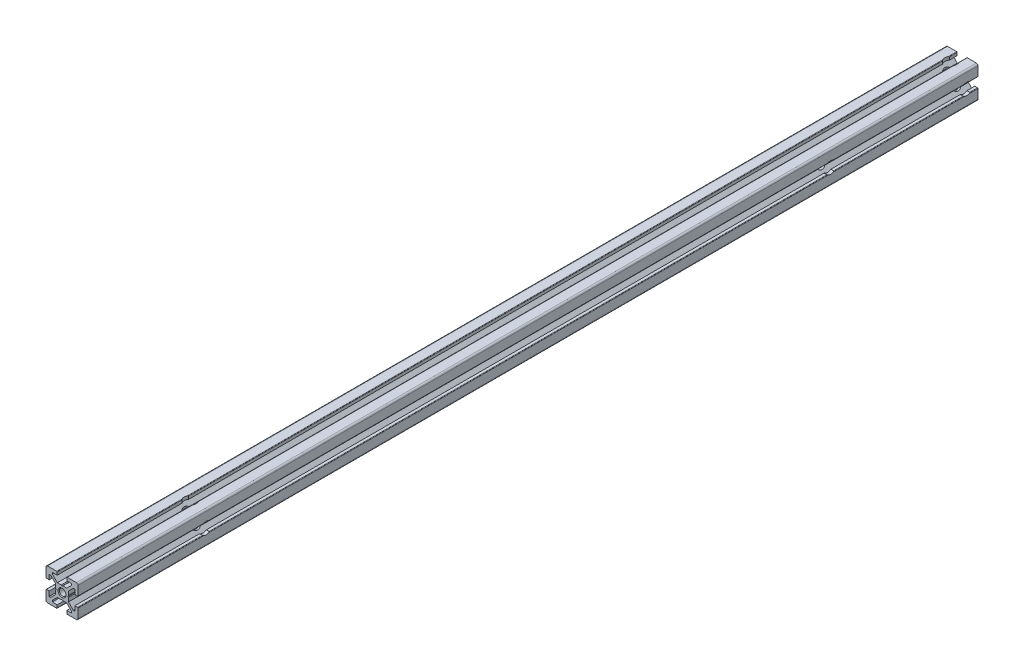
SolidWorks part; units mm, degrees
material "6063-T5"
ref_plane "Front Plane" through (0, 0, 0) normal (0, 0, 1) x (1, 0, 0)
ref_plane "Top Plane" through (0, 0, 0) normal (0, 1, 0) x (1, 0, 0)
ref_plane "Right Plane" through (0, 0, 0) normal (1, 0, 0) x (0, 0, -1)
ref_plane "Plane1" through (0, 0, 0) normal (0, 0, 1) x (1, 0, 0)
sketch "Sketch1" plane through (0, 0, 0) normal (0, 0, 1) x (1, 0, 0)
  line L0 (-10, 9) -> (-10, 3.3)
  line L1 (-9.7, 3) -> (-8, 3)
  line L2 (-8, 3) -> (-8, 6)
  line L3 (-8, 6) -> (-7.0607, 6)
  line L4 (-7.0607, 6) -> (-4, 2.9393)
  line L5 (-4, 2.9393) -> (-4, 0.5196)
  line L6 (-4, 0.5196) -> (-3.7, 0)
  line L7 (-3.7, 0) -> (-4, -0.5196)
  line L8 (-4, -0.5196) -> (-4, -2.9393)
  line L9 (-4, -2.9393) -> (-7.0607, -6)
  line L10 (-7.0607, -6) -> (-8, -6)
  line L11 (-8, -6) -> (-8, -3)
  line L12 (-8, -3) -> (-9.7, -3)
  line L13 (-10, -3.3) -> (-10, -9)
  line L14 (-9, -10) -> (-3.3, -10)
  line L15 (-3, -9.7) -> (-3, -8)
  line L16 (-3, -8) -> (-6, -8)
  line L17 (-6, -8) -> (-6, -7.0607)
  line L18 (-6, -7.0607) -> (-2.9393, -4)
  line L19 (-2.9393, -4) -> (-0.5196, -4)
  line L20 (-0.5196, -4) -> (0, -3.7)
  line L21 (0, -3.7) -> (0.5196, -4)
  line L22 (0.5196, -4) -> (2.9393, -4)
  line L23 (2.9393, -4) -> (6, -7.0607)
  line L24 (6, -7.0607) -> (6, -8)
  line L25 (6, -8) -> (3, -8)
  line L26 (3, -8) -> (3, -9.7)
  line L27 (3.3, -10) -> (9, -10)
  line L28 (10, -9) -> (10, -3.3)
  line L29 (9.7, -3) -> (8, -3)
  line L30 (8, -3) -> (8, -6)
  line L31 (8, -6) -> (7.0606, -6)
  line L32 (7.0606, -6) -> (4, -2.9393)
  line L33 (4, -2.9393) -> (4, -0.5196)
  line L34 (4, -0.5196) -> (3.7, 0)
  line L35 (3.7, 0) -> (4, 0.5196)
  line L36 (4, 0.5196) -> (4, 2.9393)
  line L37 (4, 2.9393) -> (7.0607, 6)
  line L38 (7.0607, 6) -> (8, 6)
  line L39 (8, 6) -> (8, 3)
  line L40 (8, 3) -> (9.7, 3)
  line L41 (10, 3.3) -> (10, 9)
  line L42 (9, 10) -> (3.3, 10)
  line L43 (3, 9.7) -> (3, 8)
  line L44 (3, 8) -> (6, 8)
  line L45 (6, 8) -> (6, 7.0607)
  line L46 (6, 7.0607) -> (2.9393, 4)
  line L47 (2.9393, 4) -> (0.5196, 4)
  line L48 (0.5196, 4) -> (0, 3.7)
  line L49 (0, 3.7) -> (-0.5196, 4)
  line L50 (-0.5196, 4) -> (-2.9394, 4)
  line L51 (-2.9394, 4) -> (-6, 7.0606)
  line L52 (-6, 7.0606) -> (-6, 8)
  line L53 (-6, 8) -> (-3, 8)
  line L54 (-3, 8) -> (-3, 9.7)
  line L55 (-3.3, 10) -> (-9, 10)
  arc A0 (-10, 3.3) -> (-9.7, 3) centre (-9.7, 3.3) ccw
  arc A1 (-9.7, -3) -> (-10, -3.3) centre (-9.7, -3.3) ccw
  arc A2 (-10, -9) -> (-9, -10) centre (-9, -9) ccw
  arc A3 (-3.3, -10) -> (-3, -9.7) centre (-3.3, -9.7) ccw
  arc A4 (3, -9.7) -> (3.3, -10) centre (3.3, -9.7) ccw
  arc A5 (9, -10) -> (10, -9) centre (9, -9) ccw
  arc A6 (10, -3.3) -> (9.7, -3) centre (9.7, -3.3) ccw
  arc A7 (9.7, 3) -> (10, 3.3) centre (9.7, 3.3) ccw
  arc A8 (10, 9) -> (9, 10) centre (9, 9) ccw
  arc A9 (3.3, 10) -> (3, 9.7) centre (3.3, 9.7) ccw
  arc A10 (-3, 9.7) -> (-3.3, 10) centre (-3.3, 9.7) ccw
  arc A11 (-9, 10) -> (-10, 9) centre (-9, 9) ccw
extrude "Boss-Extrude1" add sketch "Sketch1" against normal blind 562
ref_plane "Plane2" through (0, 0, 0) normal (1, 0, 0) x (0, 0, -1)
sketch "Sketch2" plane through (0, 0, 0) normal (1, 0, 0) x (0, 0, -1)
  line L0 (0, 0) -> (0, 2.5)
  line L1 (0, 2.5) -> (0.433, 2.067)
  line L2 (0.433, 2.067) -> (562, 2.067)
  line L3 (562, 2.067) -> (562, 0)
  line L4 (562, 0) -> (0, 0)
  line L5 (562, 0) -> (0, 0) construction
revolve "Cut-Revolve1" cut sketch "Sketch2" angle 360 about L5
cosmetic thread "Cosmetic Thread1" parameters "D1"=15, "D2"=5
ref_plane "Plane3" through (0, 0, 0) normal (1, 0, 0) x (0, 0, -1)
sketch "Sketch3" plane through (0, 0, 0) normal (1, 0, 0) x (0, 0, -1)
  line L0 (562, 0.5196) -> (562, 2.9393) construction
  line L1 (562, 0) -> (0, 0) construction
  circle A0 centre (555, 0) radius 3.675
  dimension "D1" = 7
  dimension "D2" = 7.35
extrude "Cut-Extrude1" cut sketch "Sketch3" against normal blind 10 and the other way blind 10
ref_plane "Plane4" through (0, 0, 0) normal (0, 1, 0) x (1, 0, 0)
sketch "Sketch4" plane through (0, 0, 0) normal (0, 1, 0) x (1, 0, 0)
  line L0 (-2.9393, 562) -> (-0.5196, 562) construction
  line L1 (0, 562) -> (0, 0) construction
  circle A0 centre (0, 555) radius 3.675
  dimension "D1" = 7.35
  dimension "D2" = 7
extrude "Cut-Extrude2" cut sketch "Sketch4" against normal blind 10 and the other way blind 10
ref_plane "Plane5" through (0, 0, 0) normal (1, 0, 0) x (0, 0, -1)
sketch "Sketch5" plane through (0, 0, 0) normal (1, 0, 0) x (0, 0, -1)
  line L1 (551.325, 0) -> (0, 0) construction
  line L2 (0, 0.5196) -> (0, 2.9393) construction
  circle A0 centre (470, 0) radius 3.6751
  dimension "D1" = 470
  dimension "D2" = 7.3502
extrude "Cut-Extrude3" cut sketch "Sketch5" against normal blind 10 and the other way blind 10
ref_plane "Plane6" through (0, 0, 0) normal (1, 0, 0) x (0, 0, -1)
sketch "Sketch6" plane through (0, 0, 0) normal (1, 0, 0) x (0, 0, -1)
  line L1 (466.3249, 0) -> (0, 0) construction
  line L2 (0, 0.5196) -> (0, 2.9393) construction
  circle A0 centre (80, 0) radius 3.6752
  dimension "D1" = 80
  dimension "D2" = 7.3504
extrude "Cut-Extrude4" cut sketch "Sketch6" against normal blind 10 and the other way blind 10
ref_plane "Plane7" through (0, 0, 0) normal (0, 1, 0) x (1, 0, 0)
sketch "Sketch7" plane through (0, 0, 0) normal (0, 1, 0) x (1, 0, 0)
  line L0 (0, 551.325) -> (0, 0) construction
  line L2 (0.5196, 0) -> (2.9393, 0) construction
  circle A0 centre (0, 80) radius 3.6752
  dimension "D1" = 7.3504
  dimension "D2" = 80
extrude "Cut-Extrude5" cut sketch "Sketch7" against normal blind 10 and the other way blind 10
